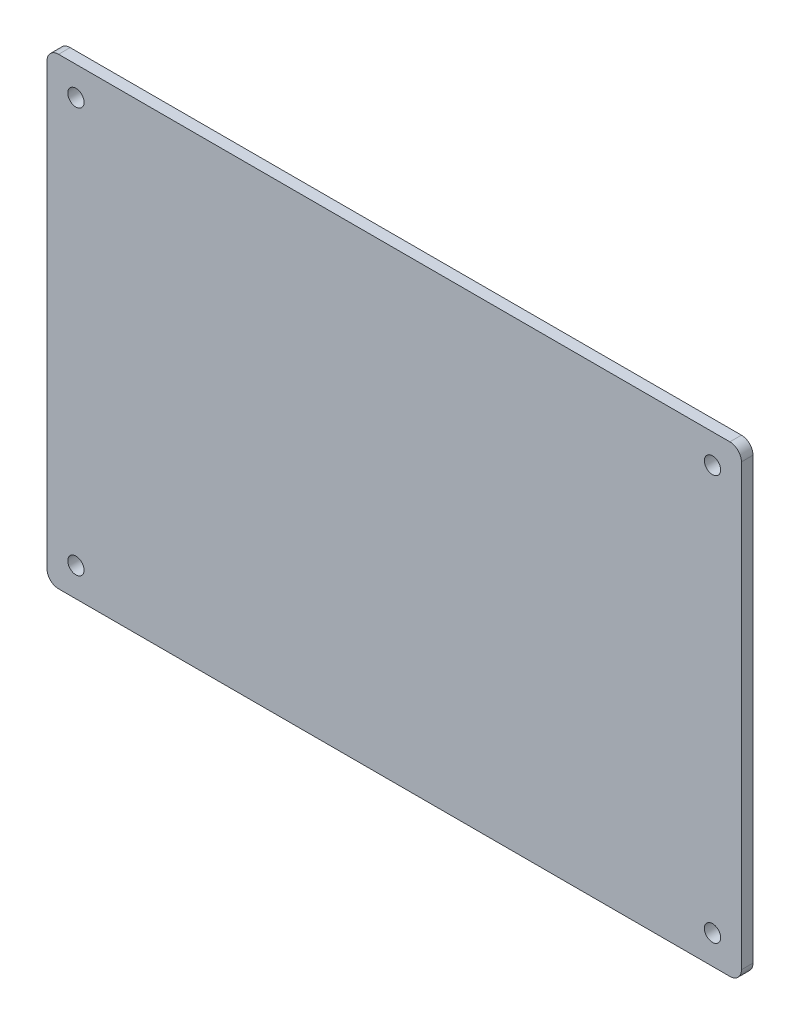
SolidWorks part; units mm, degrees
material "Circuit imprimé de calcul, simple"
ref_plane "Plan de face" through (0, 0, 0) normal (0, 0, 1) x (1, 0, 0)
ref_plane "Plan de dessus" through (0, 0, 0) normal (0, 1, 0) x (1, 0, 0)
ref_plane "Plan de droite" through (0, 0, 0) normal (1, 0, 0) x (0, 0, -1)
sketch "Esquisse1" plane through (0, 0, 0) normal (0, 0, 1) x (1, 0, 0)
  line L1 (0, 0) -> (120, 0)
  line L2 (0, 0) -> (0, 80)
  line L3 (0, 80) -> (120, 80)
  line L4 (120, 0) -> (120, 80)
  dimension "D1" = 80
  dimension "D2" = 120
extrude "Boss.-Extru.1" add sketch "Esquisse1" along normal blind 2
fillet "Congé4" radius 2 1 edges at (0, 0, 1)
fillet "Congé5" radius 2 3 edges at (120, 0, 1) (120, 80, 1) (0, 80, 1)
sketch "Esquisse2" plane through (0, 0, 0) normal (0, 0, 1) x (1, 0, 0)
  line L0 (0, 78) -> (0, 2) construction
  line L1 (118, 80) -> (2, 80) construction
  line L2 (0, 40) -> (21.2424, 40)
  line L3 (60, 0) -> (60, 12.2895)
  line L4 (2, 0) -> (118, 0) construction
  circle A0 centre (5, 75) radius 1.4073
  circle A1 centre (5, 5) radius 1.4073
  circle A2 centre (115, 5) radius 1.4073
  circle A3 centre (115, 75) radius 1.4073
  point P18 (0, 0)
  point P19 (0, 0)
  dimension "D1" = 5
  dimension "D2" = 5
extrude "Enlèv. mat.-Extru.1" cut sketch "Esquisse2" along normal through all contours A2 | A3 | A0 | A1
